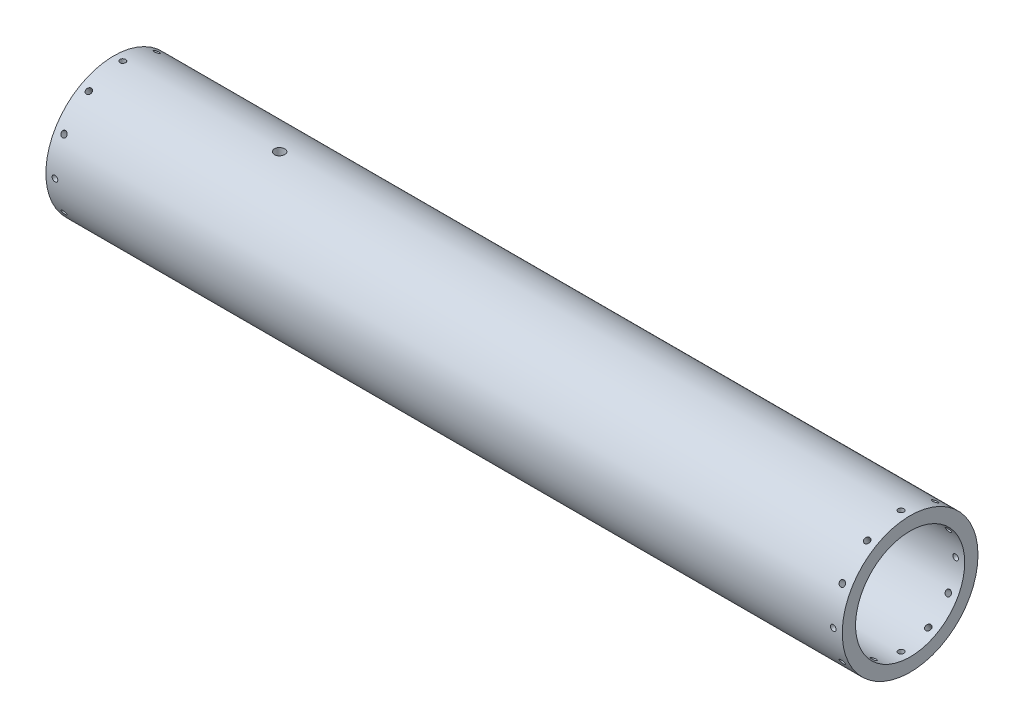
SolidWorks part; units mm, degrees
material "6061-T6 (SS)"
ref_plane "Front Plane" through (0, 0, 0) normal (0, 0, 1) x (1, 0, 0)
ref_plane "Top Plane" through (0, 0, 0) normal (0, 1, 0) x (1, 0, 0)
ref_plane "Right Plane" through (0, 0, 0) normal (1, 0, 0) x (0, 0, -1)
sketch "Sketch1" plane through (0, 0, 0) normal (1, 0, 0) x (0, 0, -1)
  circle A0 centre (0, 0) radius 45.9486
  circle A1 centre (0, 0) radius 57.15
  dimension "D1" = 91.8972
  dimension "D2" = 114.3
extrude "Boss-Extrude1" add sketch "Sketch1" along normal blind 670.56
sketch "Sketch4" plane through (0, 0, 0) normal (0, 0, 1) x (1, 0, 0)
  line L0 (0, 0) -> (0, 88.0135) construction
  line L1 (0, 57.15) -> (0, -57.15) construction
  line L2 (0, -55) -> (0, 55) construction
  line L3 (0, 0) -> (-48.5735, 0) construction
ref_plane "Plane1" through (0, 57.15, 0) normal (0, 1, 0) x (1, 0, 0)
sketch "Sketch6" plane through (0, 57.15, 0) normal (0, 1, 0) x (1, 0, 0)
  line L0 (0, 57.15) -> (0, -57.15) construction
  circle A0 centre (7.62, 0) radius 2.413
  dimension "D1" = 4.826
  dimension "D2" = 7.62
extrude "Cut-Extrude1" cut sketch "Sketch6" against normal blind 15.24
sketch "Sketch7" plane through (0, 57.15, 0) normal (0, 1, 0) x (1, 0, 0)
  line L0 (670.56, -57.15) -> (670.56, 57.15) construction
  circle A0 centre (662.94, 0) radius 2.413
  point P8 (670.56, 0)
  dimension "D2" = 4.826
  dimension "D1" = 7.62
extrude "Cut-Extrude2" cut sketch "Sketch7" against normal blind 15.24
pattern_circular "CirPattern2" count 12 over 360 about axis through (670.56, 0, 0) along (1, 0, 0) of "Cut-Extrude2"
pattern_circular "CirPattern3" count 12 over 360 about axis through (0, 0, 0) along (-1, 0, 0) of "Cut-Extrude1"
sketch "Sketch8" plane through (0, 57.15, 0) normal (0, 1, 0) x (1, 0, 0)
  line L0 (0, 57.15) -> (0, -57.15) construction
  circle A0 centre (139.7, 0) radius 4.3053
  dimension "D2" = 8.6106
  dimension "D1" = 139.7
extrude "Cut-Extrude3" cut sketch "Sketch8" against normal through all
